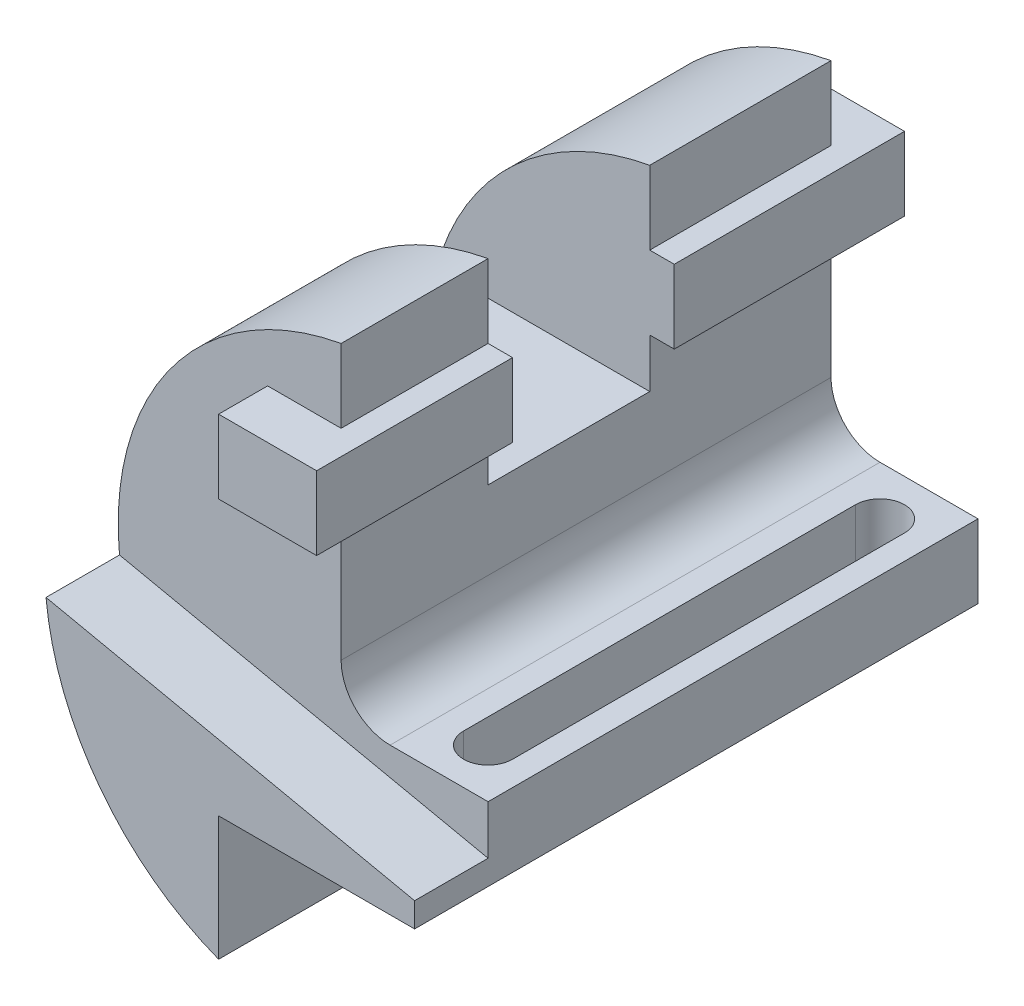
SolidWorks part; units mm, degrees
material "1060 Alloy"
ref_plane "Front Plane" through (0, 0, 0) normal (0, 0, 1) x (1, 0, 0)
ref_plane "Top Plane" through (0, 0, 0) normal (0, 1, 0) x (1, 0, 0)
ref_plane "Right Plane" through (0, 0, 0) normal (1, 0, 0) x (0, 0, -1)
sketch "Sketch1" plane through (0, 0, 0) normal (0, 0, 1) x (1, 0, 0)
  line L0 (0, 0) -> (40, 0)
  line L1 (40, 0) -> (40, 15)
  line L3 (10, 15) -> (10, 81)
  line L4 (0, 0) -> (0, -25.3628)
  line L5 (40, 15) -> (10, 15)
  arc A0 (10, 81) -> (0, -25.3628) centre (20, 26.4083) ccw
  point P5 (10, 25.5)
  point P9 (0, 0)
  point P10 (10, 15)
  point P11 (0, 0)
  point P12 (17.7023, 26.0371)
  dimension "D4" = 55.5
  dimension "D6" = 10
  dimension "D1" = 15
  dimension "D2" = 40
  dimension "D3" = 30
  dimension "D5" = 66
extrude "Boss-Extrude1" add sketch "Sketch1" along normal blind 115
sketch "Sketch2" plane through (0, 0, 115) normal (0, 0, 1) x (1, 0, 0)
  line L0 (40, 5) -> (-35.235, 20.9917)
  line L1 (40, 0) -> (40, 15) construction
  line L7 (0, -25.3628) -> (0, 0)
  line L8 (0, 0) -> (40, 0)
  line L9 (40, 0) -> (40, 15)
  line L10 (40, 15) -> (10, 15)
  line L11 (10, 15) -> (10, 81)
  line L14 (40, 5) -> (40, 15)
  line L16 (10, 15) -> (10, 81)
  line L17 (40, 15) -> (10, 15)
  arc A4 (10, 81) -> (0, -25.3628) centre (20, 26.4083) ccw
  arc A6 (10, 81) -> (-35.235, 20.9917) centre (20, 26.4083) ccw
  point P4 (0, 0)
  dimension "D1" = 78
  dimension "D2" = 5
  dimension "D3" = 0
extrude "Cut-Extrude1" cut sketch "Sketch2" against normal blind 15 and the other way through all
sketch "Sketch3" plane through (0, 0, 0) normal (0, 0, -1) x (-1, 0, 0)
  line L0 (-15, 66) -> (5, 66)
  line L1 (5, 66) -> (5, 51)
  line L2 (5, 51) -> (-15, 51)
  line L3 (-15, 51) -> (-15, 66)
  line L6 (-10, 15) -> (-10, 81) construction
  dimension "D4" = 15
  dimension "D1" = 5
  dimension "D2" = 15
  dimension "D3" = 20
extrude "Boss-Extrude2" add sketch "Sketch3" against normal offset from surface 5 and the other way blind 10 up to face at (12.953, 3.1621, 115)
sketch "Sketch4" plane through (10, 0, 0) normal (1, 0, 0) x (0, 0, -1)
  line L0 (-70, 81) -> (-37, 81)
  line L1 (-100, 81) -> (0, 81) construction
  line L2 (-37, 81) -> (-37, 41)
  line L3 (-37, 41) -> (-70, 41)
  line L4 (-70, 41) -> (-70, 81)
  line L5 (-100, 51) -> (0, 51) construction
  dimension "D1" = 10
  dimension "D2" = 33
  dimension "D3" = 30
extrude "Cut-Extrude2" cut sketch "Sketch4" against normal through all both and the other way through all
sketch "Sketch6" plane through (0, 15, 0) normal (0, 1, 0) x (1, 0, 0)
  line L0 (30, -10) -> (30, -90) construction
  line L1 (35, -10) -> (35, -90)
  line L2 (25, -10) -> (25, -90)
  line L3 (-35.235, -100) -> (40, -100) construction
  arc A0 (35, -10) -> (25, -10) centre (30, -10) ccw
  arc A1 (25, -90) -> (35, -90) centre (30, -90) ccw
  point P2 (30, -50)
  point P11 (32.1452, -93.3962)
  dimension "D1" = 5
  dimension "D2" = 80
  dimension "D3" = 10
  dimension "D4" = 10
extrude "Cut-Extrude4" cut sketch "Sketch6" against normal through all both and the other way through all
fillet "Fillet1" radius 10 1 edges at (10, 15, 50)
equation "\"A\"= 55.5mm"
equation "\"B\"= 66mm"
equation "\"C\"= 33mm"
